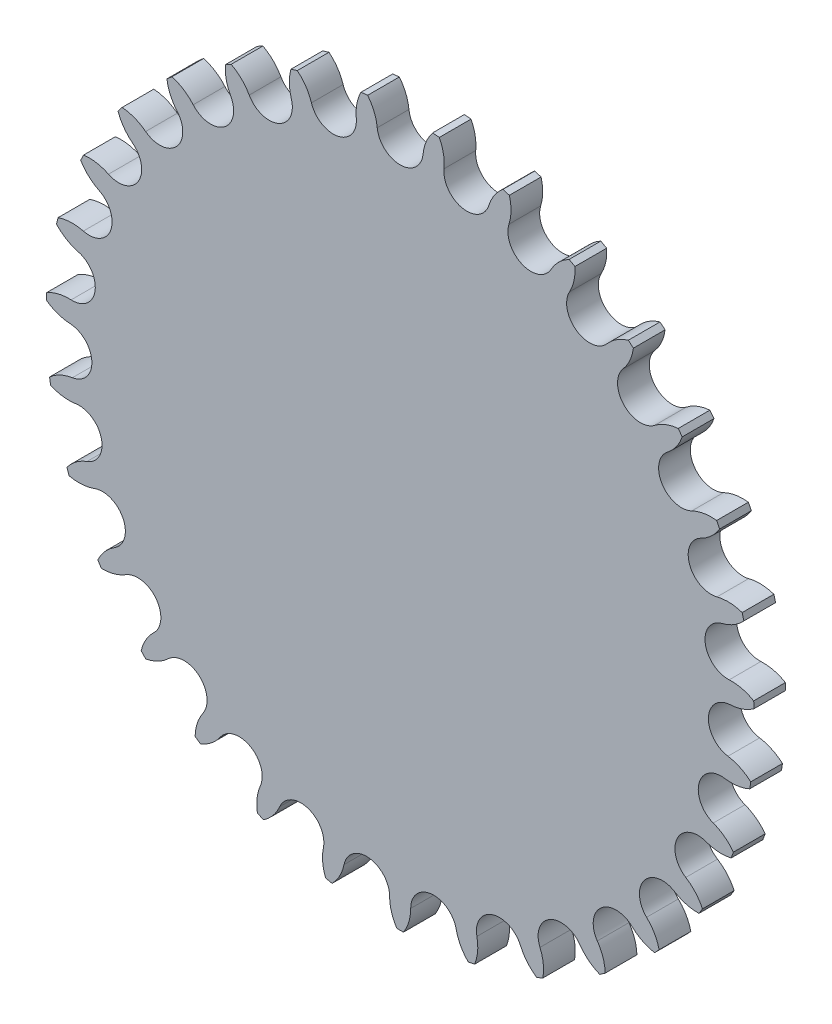
SolidWorks part; units mm, degrees
material "AISI 1020"
ref_plane "Спереди" through (0, 0, 0) normal (0, 0, 1) x (1, 0, 0)
ref_plane "Сверху" through (0, 0, 0) normal (0, 1, 0) x (1, 0, 0)
ref_plane "Справа" through (0, 0, 0) normal (1, 0, 0) x (0, 0, -1)
sketch "Эскиз1" plane through (0, 0, 0) normal (0, 0, 1) x (1, 0, 0)
  line L4 (0, 0) -> (0, 62.7667)
  line L5 (0, 62.7667) -> (12.6348, 61.4818)
  line L6 (12.6348, 61.4818) -> (0, 0)
  circle A1 centre (0, 62.7667) radius 4.255
  circle A2 centre (12.6348, 61.4818) radius 4.255
  circle A3 centre (0, 0) radius 67.0217 construction
  dimension "D6" = 8.51
  dimension "D1" = 134.0434
  dimension "D5" = 11.613
  dimension "D7" = 12.7
sketch "Эскиз2" plane through (0, 0, 0) normal (0, 0, 1) x (1, 0, 0)
  line L0 (0, 0) -> (0, 58.4117)
  line L1 (0, 0) -> (11.7582, 57.216)
  line L4 (12.6348, 61.4818) -> (0, 0) construction
  arc A0 (8.3022, 61.9224) -> (7.4067, 66.6112) centre (0, 62.7667) ccw
  arc A1 (0, 67.0217) -> (13.4914, 65.6497) centre (0, 0) cw construction
  circle A2 centre (0, 62.7667) radius 4.255 construction
  circle A3 centre (12.6348, 61.4818) radius 4.255 construction
  circle A5 centre (0, 62.7667) radius 4.355
  arc A6 (0, 58.4117) -> (4.3327, 62.3261) centre (0, 62.7667) ccw
  arc A7 (6.1537, 66.7386) -> (4.3327, 62.3261) centre (12.6348, 61.4818) ccw
  circle A8 centre (12.6348, 61.4818) radius 4.355
  arc A9 (8.3022, 61.9224) -> (11.7582, 57.216) centre (12.6348, 61.4818) ccw
  arc A10 (6.1537, 66.7386) -> (7.4067, 66.6112) centre (0, 0) cw
  point P6 (0, 0)
  dimension "D1" = 0.1
  dimension "D2" = 0.1
extrude "Бобышка-Вытянуть1" add sketch "Эскиз2" along normal blind 6
pattern_circular "Круговой массив1" count 31 over 360 about axis through (0, 0, 0) along (0, 0, 1) of "Бобышка-Вытянуть1"
sketch "Эскиз3" plane through (0, 0, 6) normal (0, 0, 1) x (1, 0, 0)
  line L0 (0, 0) -> (0, 30) construction
  line L1 (0, 0) -> (25.9808, 15) construction
  circle A0 centre (0, 0) radius 17.5
  circle A1 centre (0, 0) radius 30 construction
  circle A2 centre (0, 30) radius 4
  circle A3 centre (25.9808, 15) radius 4
  circle A4 centre (25.9808, -15) radius 4
  circle A5 centre (0, -30) radius 4
  circle A6 centre (-25.9808, -15) radius 4
  circle A7 centre (-25.9808, 15) radius 4
  dimension "D1" = 35
  dimension "D2" = 60
  dimension "D3" = 8
  dimension "D5" = 60
  dimension "D6" = 30
  dimension "D4" = 6
extrude "Вырез-Вытянуть1" [suppressed] cut sketch "Эскиз3" against normal through all
equation "\"D5@Эскиз1\"=360/\"_kol-vo\""
equation "\"_kol-vo\"= 31"
equation "\"_Pitch\"=12.7"
equation "\"_d1_max\"= 8.51"
equation "\"_d1_min\"= 7.75"
equation "\"_d2_max\"= 4.45"
equation "\"_T_max\"= 1.6"
equation "\"_h2\"= 11.8"
equation "\"_L_max\"= 16.85"
equation "\"_Lc_max\"= 18.1"
equation "\"D6@Эскиз1\"=\"_d1_max\""
equation "\"D1@Круговой массив1\"=\"_kol-vo\""
equation "\"D7@Эскиз1\"=\"_Pitch\""
